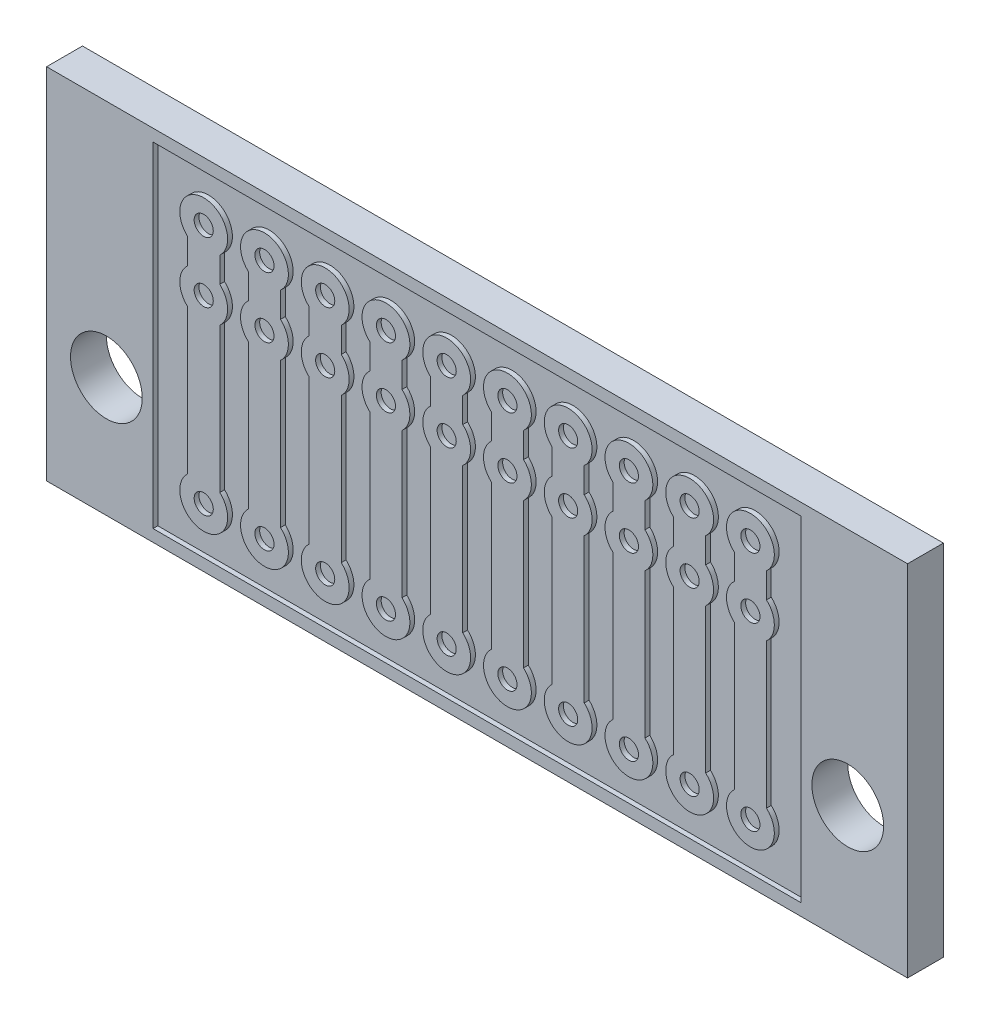
SolidWorks part; units mm, degrees
ref_plane "Front Plane" through (0, 0, 0) normal (0, 0, 1) x (1, 0, 0)
ref_plane "Top Plane" through (0, 0, 0) normal (0, 1, 0) x (1, 0, 0)
ref_plane "Right Plane" through (0, 0, 0) normal (1, 0, 0) x (0, 0, -1)
sketch "Sketch1" plane through (0, 0, 0) normal (0, 0, 1) x (1, 0, 0)
  line L41 (-18, 7.5) -> (18, 7.5)
  line L42 (-18, 7.5) -> (-18, -7.5)
  line L43 (-18, -7.5) -> (18, -7.5)
  line L44 (18, 7.5) -> (18, -7.5)
  line L45 (-18, 7.5) -> (18, -7.5) construction
  line L46 (-18, -7.5) -> (18, 7.5) construction
  point P1 (0, 0)
extrude "Boss-Extrude3" add sketch "Sketch1" along normal blind 1.5
sketch "Sketch3" plane through (0, 0, 1.5) normal (0, 0, 1) x (1, 0, 0)
  line L0 (3.1389, -4.2987) -> (3.1389, 1.7587)
  line L1 (4.4811, -4.2987) -> (4.4811, 1.7587)
  line L2 (0.5989, 3.2413) -> (0.5989, 4.2987)
  line L3 (0.5989, -4.2987) -> (0.5989, 1.7587)
  line L4 (3.1389, 3.2413) -> (3.1389, 4.2987)
  line L5 (4.4811, 3.2413) -> (4.4811, 4.2987)
  line L6 (1.9411, 3.2413) -> (1.9411, 4.2987)
  line L7 (5.6789, -4.2987) -> (5.6789, 1.7587)
  line L8 (7.0211, -4.2987) -> (7.0211, 1.7587)
  line L9 (5.6789, 3.2413) -> (5.6789, 4.2987)
  line L10 (1.9411, -4.2987) -> (1.9411, 1.7587)
  line L11 (7.0211, 3.2413) -> (7.0211, 4.2987)
  line L12 (8.2189, -4.2987) -> (8.2189, 1.7587)
  line L13 (9.5611, -4.2987) -> (9.5611, 1.7587)
  line L14 (8.2189, 3.2413) -> (8.2189, 4.2987)
  line L15 (9.5611, 3.2413) -> (9.5611, 4.2987)
  line L16 (10.7589, -4.2987) -> (10.7589, 1.7587)
  line L17 (12.1011, -4.2987) -> (12.1011, 1.7587)
  line L18 (10.7589, 3.2413) -> (10.7589, 4.2987)
  line L19 (12.1011, 3.2413) -> (12.1011, 4.2987)
  line L20 (-0.5989, -4.2987) -> (-0.5989, 1.7587)
  line L21 (-1.9411, -4.2987) -> (-1.9411, 1.7587)
  line L22 (-1.9411, 3.2413) -> (-1.9411, 4.2987)
  line L23 (-0.5989, 3.2413) -> (-0.5989, 4.2987)
  line L24 (-3.1389, -4.2987) -> (-3.1389, 1.7587)
  line L25 (-4.4811, -4.2987) -> (-4.4811, 1.7587)
  line L26 (-4.4811, 3.2413) -> (-4.4811, 4.2987)
  line L27 (-3.1389, 3.2413) -> (-3.1389, 4.2987)
  line L28 (-5.6789, -4.2987) -> (-5.6789, 1.7587)
  line L29 (-7.0211, -4.2987) -> (-7.0211, 1.7587)
  line L30 (-7.0211, 3.2413) -> (-7.0211, 4.2987)
  line L31 (-5.6789, 3.2413) -> (-5.6789, 4.2987)
  line L32 (-8.2189, -4.2987) -> (-8.2189, 1.7587)
  line L33 (-9.5611, -4.2987) -> (-9.5611, 1.7587)
  line L34 (-9.5611, 3.2413) -> (-9.5611, 4.2987)
  line L35 (-8.2189, 3.2413) -> (-8.2189, 4.2987)
  line L36 (-10.7589, -4.2987) -> (-10.7589, 1.7587)
  line L37 (-12.1011, -4.2987) -> (-12.1011, 1.7587)
  line L38 (-12.1011, 3.2413) -> (-12.1011, 4.2987)
  line L39 (-10.7589, 3.2413) -> (-10.7589, 4.2987)
  line L40 (18, 7.5) -> (-18, 7.5) construction
  line L41 (-13.5487, -7) -> (13.5487, -7)
  line L42 (-13.5487, -7) -> (-13.5487, 7)
  line L43 (-13.5487, 7) -> (13.5487, 7)
  line L44 (13.5487, -7) -> (13.5487, 7)
  arc A0 (3.81, -6.04) -> (4.4811, -4.2987) centre (3.81, -5.04) ccw
  arc A1 (3.1389, -4.2987) -> (3.81, -6.04) centre (3.81, -5.04) ccw
  arc A2 (4.4811, 1.7587) -> (4.4811, 3.2413) centre (3.81, 2.5) ccw
  arc A3 (1.27, 6.04) -> (0.5989, 4.2987) centre (1.27, 5.04) ccw
  arc A4 (0.5989, 3.2413) -> (0.5989, 1.7587) centre (1.27, 2.5) ccw
  arc A5 (0.5989, -4.2987) -> (1.27, -6.04) centre (1.27, -5.04) ccw
  arc A6 (1.9411, 4.2987) -> (1.27, 6.04) centre (1.27, 5.04) ccw
  arc A7 (3.1389, 3.2413) -> (3.1389, 1.7587) centre (3.81, 2.5) ccw
  arc A8 (1.9411, 1.7587) -> (1.9411, 3.2413) centre (1.27, 2.5) ccw
  arc A9 (4.4811, 4.2987) -> (3.81, 6.04) centre (3.81, 5.04) ccw
  arc A10 (1.27, -6.04) -> (1.9411, -4.2987) centre (1.27, -5.04) ccw
  arc A11 (3.81, 6.04) -> (3.1389, 4.2987) centre (3.81, 5.04) ccw
  arc A12 (6.35, -6.04) -> (7.0211, -4.2987) centre (6.35, -5.04) ccw
  arc A13 (5.6789, -4.2987) -> (6.35, -6.04) centre (6.35, -5.04) ccw
  arc A14 (7.0211, 1.7587) -> (7.0211, 3.2413) centre (6.35, 2.5) ccw
  arc A15 (5.6789, 3.2413) -> (5.6789, 1.7587) centre (6.35, 2.5) ccw
  arc A16 (7.0211, 4.2987) -> (6.35, 6.04) centre (6.35, 5.04) ccw
  arc A17 (6.35, 6.04) -> (5.6789, 4.2987) centre (6.35, 5.04) ccw
  arc A18 (8.89, -6.04) -> (9.5611, -4.2987) centre (8.89, -5.04) ccw
  arc A19 (8.2189, -4.2987) -> (8.89, -6.04) centre (8.89, -5.04) ccw
  arc A20 (9.5611, 1.7587) -> (9.5611, 3.2413) centre (8.89, 2.5) ccw
  arc A21 (8.2189, 3.2413) -> (8.2189, 1.7587) centre (8.89, 2.5) ccw
  arc A22 (9.5611, 4.2987) -> (8.89, 6.04) centre (8.89, 5.04) ccw
  arc A23 (8.89, 6.04) -> (8.2189, 4.2987) centre (8.89, 5.04) ccw
  arc A24 (11.43, -6.04) -> (12.1011, -4.2987) centre (11.43, -5.04) ccw
  arc A25 (10.7589, -4.2987) -> (11.43, -6.04) centre (11.43, -5.04) ccw
  arc A26 (12.1011, 1.7587) -> (12.1011, 3.2413) centre (11.43, 2.5) ccw
  arc A27 (10.7589, 3.2413) -> (10.7589, 1.7587) centre (11.43, 2.5) ccw
  arc A28 (12.1011, 4.2987) -> (11.43, 6.04) centre (11.43, 5.04) ccw
  arc A29 (11.43, 6.04) -> (10.7589, 4.2987) centre (11.43, 5.04) ccw
  arc A30 (-0.5989, 1.7587) -> (-0.5989, 3.2413) centre (-1.27, 2.5) ccw
  arc A31 (-1.27, -6.04) -> (-0.5989, -4.2987) centre (-1.27, -5.04) ccw
  arc A32 (-1.9411, -4.2987) -> (-1.27, -6.04) centre (-1.27, -5.04) ccw
  arc A33 (-1.9411, 3.2413) -> (-1.9411, 1.7587) centre (-1.27, 2.5) ccw
  arc A34 (-0.5989, 4.2987) -> (-1.27, 6.04) centre (-1.27, 5.04) ccw
  arc A35 (-1.27, 6.04) -> (-1.9411, 4.2987) centre (-1.27, 5.04) ccw
  arc A36 (-3.1389, 1.7587) -> (-3.1389, 3.2413) centre (-3.81, 2.5) ccw
  arc A37 (-3.81, -6.04) -> (-3.1389, -4.2987) centre (-3.81, -5.04) ccw
  arc A38 (-4.4811, -4.2987) -> (-3.81, -6.04) centre (-3.81, -5.04) ccw
  arc A39 (-4.4811, 3.2413) -> (-4.4811, 1.7587) centre (-3.81, 2.5) ccw
  arc A40 (-3.1389, 4.2987) -> (-3.81, 6.04) centre (-3.81, 5.04) ccw
  arc A41 (-3.81, 6.04) -> (-4.4811, 4.2987) centre (-3.81, 5.04) ccw
  arc A42 (-5.6789, 1.7587) -> (-5.6789, 3.2413) centre (-6.35, 2.5) ccw
  arc A43 (-6.35, -6.04) -> (-5.6789, -4.2987) centre (-6.35, -5.04) ccw
  arc A44 (-7.0211, -4.2987) -> (-6.35, -6.04) centre (-6.35, -5.04) ccw
  arc A45 (-7.0211, 3.2413) -> (-7.0211, 1.7587) centre (-6.35, 2.5) ccw
  arc A46 (-5.6789, 4.2987) -> (-6.35, 6.04) centre (-6.35, 5.04) ccw
  arc A47 (-6.35, 6.04) -> (-7.0211, 4.2987) centre (-6.35, 5.04) ccw
  arc A48 (-8.2189, 1.7587) -> (-8.2189, 3.2413) centre (-8.89, 2.5) ccw
  arc A49 (-8.89, -6.04) -> (-8.2189, -4.2987) centre (-8.89, -5.04) ccw
  arc A50 (-9.5611, -4.2987) -> (-8.89, -6.04) centre (-8.89, -5.04) ccw
  arc A51 (-9.5611, 3.2413) -> (-9.5611, 1.7587) centre (-8.89, 2.5) ccw
  arc A52 (-8.2189, 4.2987) -> (-8.89, 6.04) centre (-8.89, 5.04) ccw
  arc A53 (-8.89, 6.04) -> (-9.5611, 4.2987) centre (-8.89, 5.04) ccw
  arc A54 (-10.7589, 1.7587) -> (-10.7589, 3.2413) centre (-11.43, 2.5) ccw
  arc A55 (-11.43, -6.04) -> (-10.7589, -4.2987) centre (-11.43, -5.04) ccw
  arc A56 (-12.1011, -4.2987) -> (-11.43, -6.04) centre (-11.43, -5.04) ccw
  arc A57 (-12.1011, 3.2413) -> (-12.1011, 1.7587) centre (-11.43, 2.5) ccw
  arc A58 (-10.7589, 4.2987) -> (-11.43, 6.04) centre (-11.43, 5.04) ccw
  arc A59 (-11.43, 6.04) -> (-12.1011, 4.2987) centre (-11.43, 5.04) ccw
  point P1 (0, 2.5)
  point P163 (0, 2.5)
  dimension "D3" = 0.5
  dimension "D1" = 5
  dimension "D2" = 6
extrude "Cut-Extrude1" cut sketch "Sketch3" against normal blind 0.2
sketch "Sketch5" plane through (0, 0, 1.5) normal (0, 0, 1) x (1, 0, 0)
  line L1 (-18, -7.5) -> (18, -7.5) construction
  circle A0 centre (-15.5, -2.5) radius 1.5
  circle A1 centre (15.5, -2.5) radius 1.5
  dimension "D1" = 5
  dimension "D2" = 5
extrude "Cut-Extrude3" cut sketch "Sketch5" against normal blind 10.2
sketch "Sketch6" plane through (0, 0, 1.5) normal (0, 0, 1) x (1, 0, 0)
  circle A0 centre (-11.43, -5.04) radius 0.4
  circle A1 centre (-11.43, 2.5) radius 0.4
  circle A2 centre (-11.43, 5.04) radius 0.4
  circle A3 centre (-8.89, 5.04) radius 0.4
  circle A4 centre (-8.89, 2.5) radius 0.4
  circle A5 centre (-8.89, -5.04) radius 0.4
  circle A6 centre (-6.35, 5.04) radius 0.4
  circle A7 centre (-6.35, 2.5) radius 0.4
  circle A8 centre (-6.35, -5.04) radius 0.4
  circle A9 centre (-3.81, 5.04) radius 0.4
  circle A10 centre (-3.81, 2.5) radius 0.4
  circle A11 centre (-3.81, -5.04) radius 0.4
  circle A12 centre (-1.27, 5.04) radius 0.4
  circle A13 centre (-1.27, 2.5) radius 0.4
  circle A14 centre (-1.27, -5.04) radius 0.4
  circle A15 centre (1.27, 5.04) radius 0.4
  circle A16 centre (1.27, 2.5) radius 0.4
  circle A17 centre (1.27, -5.04) radius 0.4
  circle A18 centre (3.81, 5.04) radius 0.4
  circle A19 centre (3.81, 2.5) radius 0.4
  circle A20 centre (3.81, -5.04) radius 0.4
  circle A21 centre (6.35, 5.04) radius 0.4
  circle A22 centre (6.35, 2.5) radius 0.4
  circle A23 centre (6.35, -5.04) radius 0.4
  circle A24 centre (8.89, 5.04) radius 0.4
  circle A25 centre (8.89, 2.5) radius 0.4
  circle A26 centre (8.89, -5.04) radius 0.4
  circle A27 centre (11.43, 5.04) radius 0.4
  circle A28 centre (11.43, 2.5) radius 0.4
  circle A29 centre (11.43, -5.04) radius 0.4
  dimension "D1" = 10
extrude "Cut-Extrude4" cut sketch "Sketch6" against normal blind 0.2
